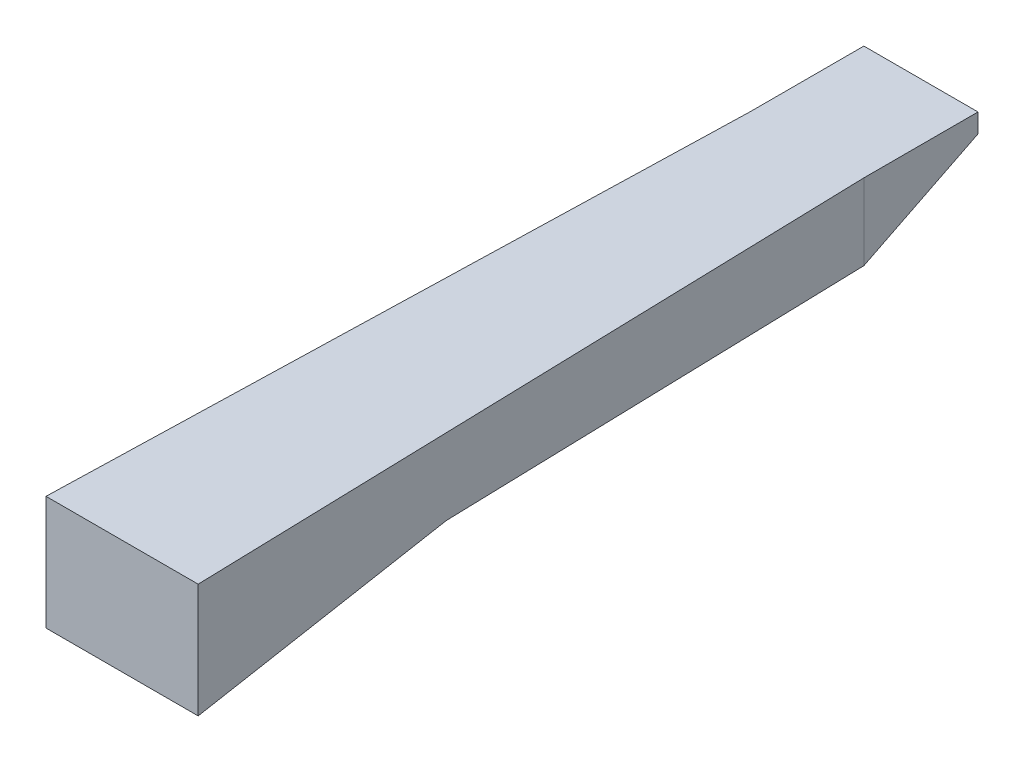
SolidWorks part; units mm, degrees
ref_plane "Front Plane" through (0, 0, 0) normal (0, 0, 1) x (1, 0, 0)
ref_plane "Top Plane" through (0, 0, 0) normal (0, 1, 0) x (1, 0, 0)
ref_plane "Right Plane" through (0, 0, 0) normal (1, 0, 0) x (0, 0, -1)
sketch "Sketch1" plane through (0, 0, 0) normal (0, 1, 0) x (1, 0, 0)
  line L0 (0, 114.3) -> (0, -114.3) construction
  line L1 (25.4, -114.3) -> (19.05, 114.3)
  line L2 (19.05, 114.3) -> (-19.05, 114.3)
  line L3 (-19.05, 114.3) -> (-25.4, -114.3)
  line L4 (-25.4, -114.3) -> (25.4, -114.3)
  line L5 (-22.225, 0) -> (22.225, 0) construction
  line L9 (-19.05, 152.4) -> (19.05, 152.4)
  line L10 (-19.05, 152.4) -> (-19.05, 114.3)
  line L12 (19.05, 152.4) -> (19.05, 114.3)
  dimension "D1" = 50.8
  dimension "D2" = 88.409
  dimension "D3" = 38.1
  dimension "D4" = 38.1
  dimension "D5" = 266.7
  dimension "D6" = 88.409
extrude "Boss-Extrude2" add sketch "Sketch1" along normal blind 50.8 contours L3 L4 L1 L2 | L12 L9 L10 L2
ref_plane "Plane2" through (0, 0, 0) normal (1, 0, 0) x (0, 0, -1)
ref_plane "Plane3" through (25.4, 0, 0) normal (1, 0, 0) x (0, 0, -1)
ref_plane "Plane4" through (0, 0, 114.3) normal (0, 0, 1) x (1, 0, 0)
sketch "Sketch11" plane through (25.4, 0, 0) normal (1, 0, 0) x (0, 0, -1)
  line L0 (-114.3, 27.94) -> (-114.3, -27.94) construction
  line L1 (114.3, 25.4) -> (-126.1612, 25.4) construction
  line L2 (114.3, 50.8) -> (114.3, 0) construction
  line L3 (-114.3, 38.1) -> (152.4, 38.1)
  line L4 (152.4, 50.8) -> (152.4, 0) construction
  line L5 (-114.3, 12.7) -> (152.4, 12.7)
  line L6 (114.3, 12.7) -> (152.4, 31.75)
  line L7 (152.4, 38.1) -> (152.4, 12.7)
  line L8 (-114.3, 38.1) -> (-114.3, 12.7)
  line L9 (-114.3, 0) -> (-29.0777, 12.7)
  line L10 (-114.3, 0) -> (114.3, 0) construction
  line L11 (-114.3, 0) -> (-114.3, 12.7)
  line L12 (-114.3, 0) -> (152.4, 0)
  line L13 (152.4, 0) -> (152.4, 12.7)
  line L14 (-114.3, 38.1) -> (-114.3, 50.8)
  line L15 (-114.3, 50.8) -> (152.4, 50.8)
  line L16 (152.4, 50.8) -> (152.4, 38.1)
  line L17 (-82.55, 38.1) -> (-82.55, 4.7314) construction
  line L18 (-82.55, 21.4157) -> (-114.3, 21.4157) construction
  line L19 (-82.55, 21.4157) -> (-29.0777, 21.4157) construction
  line L20 (-82.55, 25.4) -> (-82.55, 21.4157) construction
  circle A0 centre (-82.55, 25.4) radius 6.35
  dimension "D1" = 12.7
  dimension "D2" = 31.75
  dimension "D3" = 25.4
  dimension "D4" = 85.2223
  dimension "D5" = 6.35
extrude "Cut-Extrude6" cut sketch "Sketch11" against normal through all contours L12 L13 L5 L9 | L16 L15 L14 L3 | L7 L6 L5
sketch "Sketch14" plane through (25.4, 0, 0) normal (1, 0, 0) x (0, 0, -1)
  line L0 (-114.3, 20.955) -> (-114.3, -20.955) construction
  line L2 (-82.55, 23.8253) -> (-43.434, 23.8253) construction
  line L3 (-114.3, 38.1) -> (-114.3, 45.6549)
  line L4 (114.3, 38.1) -> (-114.3, 38.1) construction
  circle A0 centre (-82.55, 23.8253) radius 3.8454
  circle A1 centre (-43.434, 23.8253) radius 13.97
  circle A2 centre (-43.434, 23.8253) radius 43.1811
  dimension "D3" = 27.94
  dimension "D1" = 31.75
  dimension "D2" = 39.116
